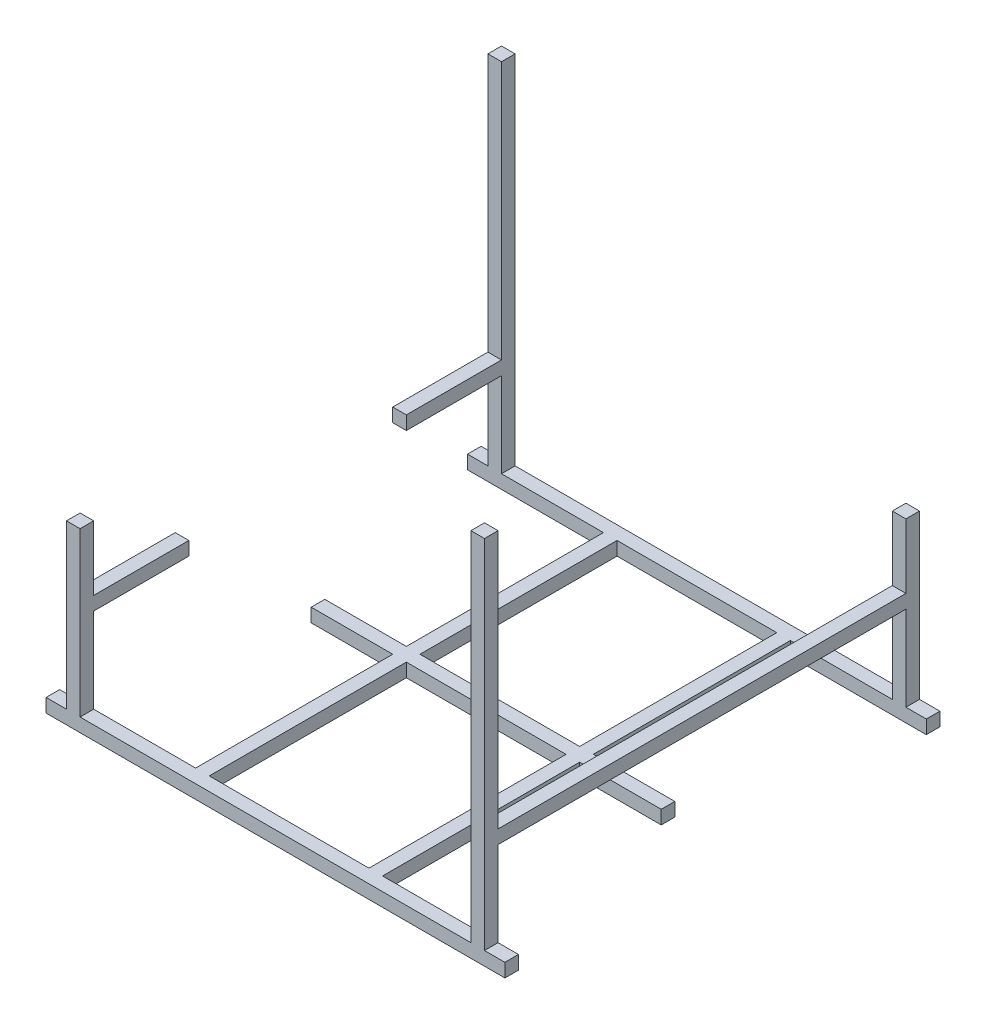
SolidWorks part; units mm, degrees
material "6061 合金"
ref_plane "前视基准面" through (0, 0, 0) normal (0, 0, 1) x (1, 0, 0)
ref_plane "上视基准面" through (0, 0, 0) normal (0, 1, 0) x (1, 0, 0)
ref_plane "右视基准面" through (0, 0, 0) normal (1, 0, 0) x (0, 0, -1)
sketch "草图1" plane through (0, 0, 0) normal (0, 1, 0) x (1, 0, 0)
  line L0 (-221.5101, -7.503) -> (-21.5101, -7.503)
  line L1 (-221.5101, 612.497) -> (453.4899, 612.497)
  line L2 (-221.5101, 612.497) -> (-221.5101, 592.497)
  line L3 (-221.5101, 592.497) -> (-21.5101, 592.497)
  line L4 (453.4899, 612.497) -> (453.4899, 592.497)
  line L5 (-221.5101, -7.503) -> (-221.5101, -27.503)
  line L6 (-221.5101, -27.503) -> (453.4899, -27.503)
  line L7 (453.4899, -7.503) -> (453.4899, -27.503)
  line L8 (253.4899, 592.497) -> (453.4899, 592.497)
  line L10 (-21.5101, 592.497) -> (-21.5101, -7.503)
  line L12 (-1.5101, 592.497) -> (-1.5101, -7.503)
  line L14 (253.4899, 592.497) -> (253.4899, -7.503)
  line L16 (233.4899, 592.497) -> (233.4899, -7.503)
  line L17 (253.4899, -7.503) -> (453.4899, -7.503)
  line L18 (-1.5101, -7.503) -> (233.4899, -7.503)
  line L19 (-1.5101, 592.497) -> (233.4899, 592.497)
  dimension "D1" = 20
  dimension "D2" = 675
  dimension "D3" = 20
  dimension "D4" = 675
  dimension "D5" = 640
  dimension "D6" = 20
  dimension "D7" = 200
  dimension "D8" = 220
  dimension "D9" = 20
extrude "凸台-拉伸1" add sketch "草图1" along normal blind 20
ref_plane "基准面1" through (-191.5101, 0, 0) normal (-1, 0, 0) x (0, 0, 1)
sketch "草图2" plane through (-191.5101, 0, 0) normal (-1, 0, 0) x (0, 0, 1)
  line L0 (27.503, 20) -> (27.503, 0) construction
  line L1 (27.503, 20) -> (7.503, 20)
  line L2 (27.503, 20) -> (27.503, 260)
  line L3 (27.503, 260) -> (7.503, 260)
  line L4 (7.503, 20) -> (7.503, 165)
  line L5 (27.503, 20) -> (7.503, 20) construction
  line L6 (-592.497, 260) -> (-592.497, 165)
  line L11 (-592.497, 20) -> (-612.497, 20)
  line L12 (-592.497, 20) -> (-592.497, 165)
  line L13 (-592.497, 260) -> (-612.497, 260)
  line L14 (-612.497, 20) -> (-612.497, 260)
  line L15 (7.503, 260) -> (7.503, 165)
  dimension "D1" = 20
  dimension "D2" = 240
  dimension "D3" = 240
extrude "凸台-拉伸4" add sketch "草图2" against normal blind 20
ref_plane "基准面4" through (115.9899, 0, 0) normal (1, 0, 0) x (0, 0, -1)
mirror "镜向3" about plane through (115.9899, 0, 0) normal (1, 0, 0) of "凸台-拉伸4"
ref_plane "基准面5" through (0, 0, -292.497) normal (0, 0, 1) x (1, 0, 0)
sketch "草图6" plane through (-191.5101, 0, 0) normal (-1, 0, 0) x (0, 0, 1)
  line L0 (27.503, 20) -> (27.503, 260) construction
  line L1 (-612.497, 165) -> (27.503, 165)
  line L2 (-612.497, 165) -> (-612.497, 145)
  line L3 (-612.497, 145) -> (27.503, 145)
  line L4 (27.503, 165) -> (27.503, 145)
  line L5 (-612.497, 20) -> (-592.497, 20) construction
  dimension "D1" = 20
  dimension "D2" = 145
extrude "凸台-拉伸6" add sketch "草图6" against normal blind 20
mirror "镜向6" about plane through (115.9899, 0, 0) normal (1, 0, 0) of "凸台-拉伸6"
sketch "Sketch1" plane through (-191.5101, 0, 0) normal (-1, 0, 0) x (0, 0, 1)
  line L0 (7.503, 165) -> (-592.497, 165) construction
  line L1 (-452.497, 165) -> (-132.497, 165)
  line L2 (-452.497, 165) -> (-452.497, 145)
  line L3 (-452.497, 145) -> (-132.497, 145)
  line L4 (-132.497, 165) -> (-132.497, 145)
  line L5 (-592.497, 145) -> (7.503, 145) construction
  line L6 (-612.497, 260) -> (-612.497, 20) construction
  line L7 (27.503, 20) -> (27.503, 260) construction
  dimension "D1" = 160
  dimension "D2" = 160
extrude "Cut-Extrude1" cut sketch "Sketch1" against normal blind 20
sketch "Sketch2" plane through (0, 0, 0) normal (0, -1, 0) x (-1, 0, 0)
  line L0 (-253.4899, 292.497) -> (-301.1658, 292.497) construction
  line L1 (-373.4899, 282.497) -> (141.5101, 282.497)
  line L2 (-373.4899, 282.497) -> (-373.4899, 302.497)
  line L3 (-373.4899, 302.497) -> (141.5101, 302.497)
  line L4 (141.5101, 282.497) -> (141.5101, 302.497)
  line L5 (-253.4899, -7.503) -> (-253.4899, 592.497) construction
  line L8 (21.5101, 592.497) -> (21.5101, -7.503) construction
  dimension "D1" = 10
  dimension "D2" = 10
  dimension "D3" = 120
  dimension "D4" = 120
extrude "Extrude1" add sketch "Sketch2" against normal blind 20
sketch "Sketch3" plane through (0, 260, 0) normal (0, 1, 0) x (1, 0, 0)
  line L4 (-191.5101, 612.497) -> (-191.5101, 592.497)
  line L5 (-191.5101, 592.497) -> (-171.5101, 592.497)
  line L6 (-171.5101, 592.497) -> (-171.5101, 612.497)
  line L7 (-171.5101, 612.497) -> (-191.5101, 612.497)
  line L8 (-191.5101, 612.497) -> (-191.5101, 592.497)
  line L9 (-191.5101, 592.497) -> (-171.5101, 592.497)
  line L10 (-171.5101, 592.497) -> (-171.5101, 612.497)
  line L11 (-171.5101, 612.497) -> (-191.5101, 612.497)
  line L12 (423.4899, -27.503) -> (423.4899, -7.503)
  line L13 (423.4899, -7.503) -> (403.4899, -7.503)
  line L14 (403.4899, -7.503) -> (403.4899, -27.503)
  line L15 (403.4899, -27.503) -> (423.4899, -27.503)
  line L16 (423.4899, -27.503) -> (423.4899, -7.503)
  line L17 (423.4899, -7.503) -> (403.4899, -7.503)
  line L18 (403.4899, -7.503) -> (403.4899, -27.503)
  line L19 (403.4899, -27.503) -> (423.4899, -27.503)
  dimension "D1" = 0
  dimension "D2" = 0
extrude "Boss-Extrude1" add sketch "Sketch3" along normal up to vertex (285 mm away)
